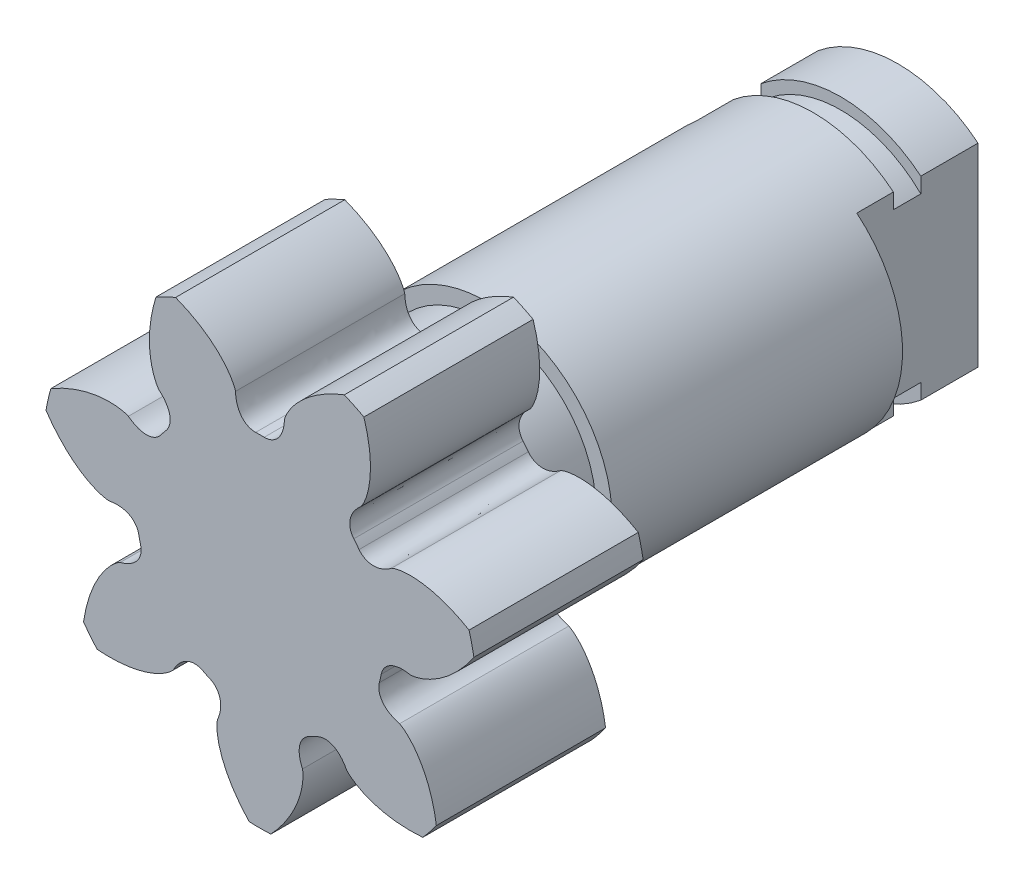
SolidWorks part; units mm, degrees
ref_plane "Спереди" through (0, 0, 0) normal (0, 0, 1) x (1, 0, 0)
ref_plane "Сверху" through (0, 0, 0) normal (0, 1, 0) x (1, 0, 0)
ref_plane "Справа" through (0, 0, 0) normal (1, 0, 0) x (0, 0, -1)
ref_axis "Ось1" through (0, 0, -88.99) along (0, 0, 1)
sketch "Gear-BaseSketch" plane through (0, 0, 0) normal (0, 0, 1) x (1, 0, 0)
  circle A0 centre (0, 0) radius 9.5
  dimension "D1" = 19
extrude "2.0 Module, 14,0000mm P.D." add sketch "Gear-BaseSketch" along normal mid plane 7.4
sketch "Tooth-Sketch; Backlash: 0,0000mm" plane through (0, 0, 0) normal (0, 0, 1) x (1, 0, 0)
  line L0 (0, 0) -> (0, 9.8668) construction
  arc A0 (-4.3272, 8.9652) -> (4.3272, 8.9652) centre (0, 0) cw
  arc A1 (-0.1857, 5.3968) -> (0.1857, 5.3968) centre (0, 0) cw
  spline S0 degree 3 poles (-1.0691, 6.5077) (-1.072, 6.5202) (-1.0783, 6.5425) (-1.0892, 6.5766) (-1.102, 6.6125) (-1.1185, 6.6544) (-1.1391, 6.7022) (-1.1642, 6.7555) (-1.1941, 6.8141) (-1.2292, 6.8778) (-1.27, 6.9463) (-1.3167, 7.0193) (-1.3696, 7.0964) (-1.4291, 7.1774) (-1.4955, 7.2618) (-1.569, 7.3493) (-1.65, 7.4396) (-1.7387, 7.5322) (-1.8352, 7.6268) (-1.9399, 7.7228) (-2.0529, 7.8199) (-2.1744, 7.9176) (-2.3045, 8.0155) (-2.4434, 8.1132) (-2.5912, 8.21) (-2.748, 8.3057) (-2.9138, 8.3996) (-3.0887, 8.4913) (-3.2727, 8.5803) (-3.4659, 8.666) (-3.6682, 8.7481) (-3.9543, 8.8535) (-4.1759, 8.923) (-4.3272, 8.9652) knots 0 0 0 0 0.009054 0.016431 0.025447 0.036102 0.048397 0.062331 0.077904 0.095116 0.113968 0.134459 0.156589 0.180359 0.205768 0.232816 0.261503 0.29183 0.323796 0.357401 0.392646 0.42953 0.468053 0.508215 0.550017 0.593458 0.638538 0.685258 0.733617 0.783615 0.835252 0.888529 1 1 1 1
  spline S1 degree 3 poles (1.0691, 6.5077) (1.072, 6.5202) (1.0783, 6.5425) (1.0892, 6.5766) (1.102, 6.6125) (1.1185, 6.6544) (1.1391, 6.7022) (1.1642, 6.7555) (1.1941, 6.8141) (1.2292, 6.8778) (1.27, 6.9463) (1.3167, 7.0193) (1.3696, 7.0964) (1.4291, 7.1774) (1.4955, 7.2618) (1.569, 7.3493) (1.65, 7.4396) (1.7387, 7.5322) (1.8352, 7.6268) (1.9399, 7.7228) (2.0529, 7.8199) (2.1744, 7.9176) (2.3045, 8.0155) (2.4434, 8.1132) (2.5912, 8.21) (2.748, 8.3057) (2.9138, 8.3996) (3.0887, 8.4913) (3.2727, 8.5803) (3.4659, 8.666) (3.6682, 8.7481) (3.9543, 8.8535) (4.1759, 8.923) (4.3272, 8.9652) knots 0 0 0 0 0.009054 0.016431 0.025447 0.036102 0.048397 0.062331 0.077904 0.095116 0.113968 0.134459 0.156589 0.180359 0.205768 0.232816 0.261503 0.29183 0.323796 0.357401 0.392646 0.42953 0.468053 0.508215 0.550017 0.593458 0.638538 0.685258 0.733617 0.783615 0.835252 0.888529 1 1 1 1
  spline S2 degree 3 poles (-1.0691, 6.5077) (-1.0673, 6.441) (-1.0573, 6.3116) (-1.0213, 6.1229) (-0.9621, 5.9433) (-0.8722, 5.7691) (-0.7367, 5.6014) (-0.5128, 5.4394) (-0.3071, 5.3944) (-0.1857, 5.3968) knots 0 0 0 0 0.126567 0.245965 0.363427 0.484115 0.615987 0.769026 1 1 1 1
  spline S3 degree 3 poles (1.0691, 6.5077) (1.0673, 6.441) (1.0573, 6.3116) (1.0213, 6.1229) (0.9621, 5.9433) (0.8722, 5.7691) (0.7367, 5.6014) (0.5128, 5.4394) (0.3071, 5.3944) (0.1857, 5.3968) knots 0 0 0 0 0.126567 0.245965 0.363427 0.484115 0.615987 0.769026 1 1 1 1
extrude "Tooth-Cut, Coarse Pitch Involute 20 deg" cut sketch "Tooth-Sketch; Backlash: 0,0000mm" against normal through all and the other way through all
pattern_circular "Круговой массив2" count 7 over 360 about axis through (0, 0, -88.99) along (0, 0, 1) of "Tooth-Cut, Coarse Pitch Involute 20 deg"
sketch "Эскиз3" plane through (0, 0, -3.7) normal (0, 0, -1) x (-1, 0, 0)
  circle A0 centre (0, 0) radius 4.8
  dimension "D1" = 9.6
extrude "Бобышка-Вытянуть2" add sketch "Эскиз3" along normal blind 2.5
sketch "Эскиз4" plane through (0, 0, 3.7) normal (0, 0, 1) x (1, 0, 0)
  line L0 (0, 7) -> (0, -7) construction
  circle A0 centre (0, 0) radius 7 construction
  dimension "D1" = 14
sketch "Эскиз5" plane through (0, 0, -6.2) normal (0, 0, -1) x (-1, 0, 0)
  circle A0 centre (0, 0) radius 5.5
  dimension "D1" = 11
extrude "Бобышка-Вытянуть3" add sketch "Эскиз5" along normal blind 18
sketch "Эскиз6" plane through (0, 0, -24.2) normal (0, 0, -1) x (-1, 0, 0)
  line L1 (-3.5, 5.5) -> (3.5, 5.5) construction
  line L2 (-3.5, 4.2426) -> (-3.5, -4.2426)
  line L3 (-3.5, -5.5) -> (3.5, -5.5) construction
  line L4 (3.5, 4.2426) -> (3.5, -4.2426)
  line L5 (-3.5, 5.5) -> (3.5, -5.5) construction
  line L6 (-3.5, -5.5) -> (3.5, 5.5) construction
  arc A0 (3.5, -4.2426) -> (3.5, 4.2426) centre (0, 0) ccw
  circle A1 centre (0, 0) radius 5.5 construction
  arc A2 (-3.5, 4.2426) -> (-3.5, -4.2426) centre (0, 0) ccw
  point P0 (0, 0)
  dimension "D1" = 7
  dimension "D2" = 3.5
  dimension "D3" = 3.5
extrude "Вырез-Вытянуть2" cut sketch "Эскиз6" against normal blind 5.3
sketch "Эскиз7" plane through (0, 0, -24.2) normal (0, 0, -1) x (-1, 0, 0)
  circle A0 centre (0, 0) radius 3
  dimension "D1" = 6
extrude "Вырез-Вытянуть3" cut sketch "Эскиз7" against normal blind 7
sketch "Эскиз8" plane through (0, 0, 0) normal (1, 0, 0) x (0, 0, -1)
  line L0 (24.2, 5.5) -> (6.2, 5.5) construction
  line L1 (20.5, 5.5) -> (21.7, 5.5)
  line L2 (20.5, 5.5) -> (20.5, 5)
  line L3 (20.5, 5) -> (21.7, 5)
  line L4 (21.7, 5.5) -> (21.7, 5)
  line L5 (0, 0) -> (29.1144, 0) construction
  line L6 (24.2, 4.2426) -> (24.2, 5.5) construction
  dimension "D1" = 10
  dimension "D2" = 2.5
  dimension "D3" = 1.2
revolve "Вырез-Повернуть1" cut sketch "Эскиз8" angle 360 about L5
